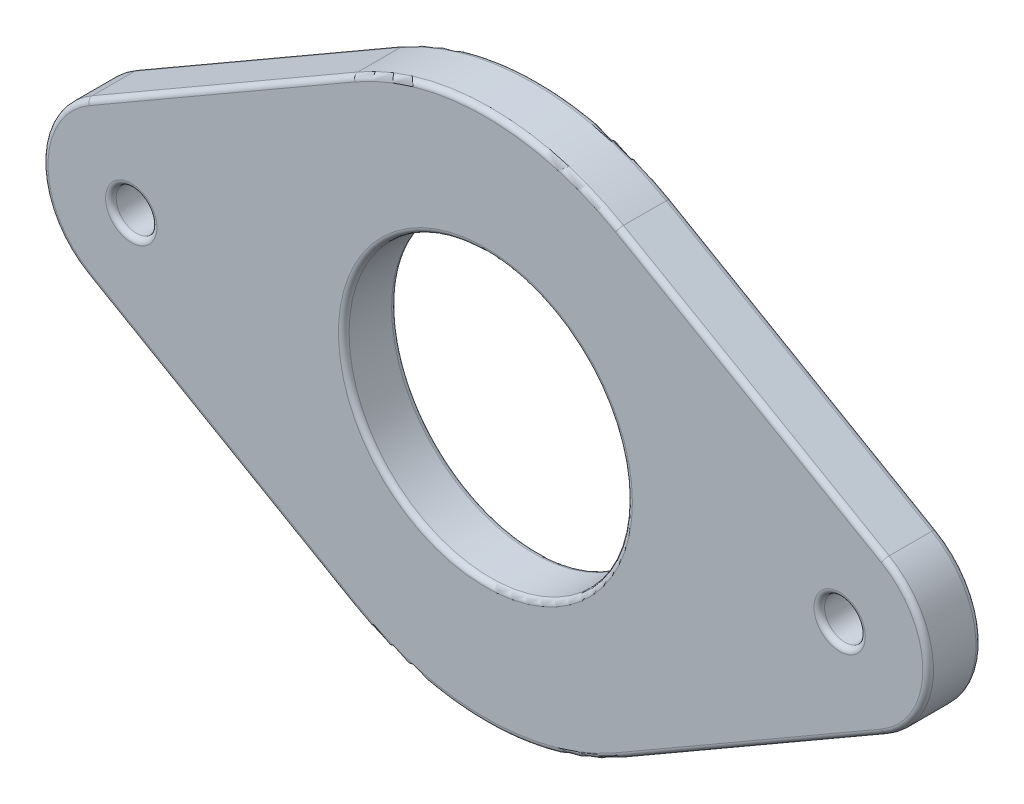
SolidWorks part; units mm, degrees
ref_plane "Front Plane" through (0, 0, 0) normal (0, 0, 1) x (1, 0, 0)
ref_plane "Top Plane" through (0, 0, 0) normal (0, 1, 0) x (1, 0, 0)
ref_plane "Right Plane" through (0, 0, 0) normal (1, 0, 0) x (0, 0, -1)
sketch "Sketch1" plane through (0, 0, 0) normal (0, 0, 1) x (1, 0, 0)
  line L0 (-20, 0) -> (20, 0) construction
  line L1 (-22.5, 4.3301) -> (-7.5, 12.9904)
  line L2 (7.5, 12.9904) -> (22.5, 4.3301)
  line L3 (-22.5, -4.3301) -> (-7.5, -12.9904)
  line L4 (7.5, -12.9904) -> (22.5, -4.3301)
  arc A0 (-7.5, -12.9904) -> (7.5, -12.9904) centre (0, 0) ccw
  circle A1 centre (-20, 0) radius 1.15
  circle A2 centre (20, 0) radius 1.15
  arc A3 (22.5, -4.3301) -> (22.5, 4.3301) centre (20, 0) ccw
  arc A4 (-22.5, 4.3301) -> (-22.5, -4.3301) centre (-20, 0) ccw
  arc A5 (7.5, 12.9904) -> (-7.5, 12.9904) centre (0, 0) ccw
  circle A6 centre (0, 0) radius 8
  dimension "D1" = 30
  dimension "D3" = 2.3
  dimension "D4" = 10
  dimension "D5" = 16
  dimension "D2" = 20
extrude "Boss-Extrude1" add sketch "Sketch1" along normal blind 3
fillet "Fillet1" radius 0.3 22 edges at (21.15, 0, 0) (-18.85, 0, 0) (8, 0, 0) (-15, -8.6603, 0) (0, -15, 0) (15, -8.6603, 0) (25, 0, 0) (15, 8.6603, 0) (0, 15, 0) (-15, 8.6603, 0) (-25, 0, 0) (21.15, 0, 3) (8, 0, 3) (-15, 8.6603, 3) (0, 15, 3) (15, 8.6603, 3) (25, 0, 3) (15, -8.6603, 3) (0, -15, 3) (-15, -8.6603, 3) (-25, 0, 3) (-18.85, 0, 3)
